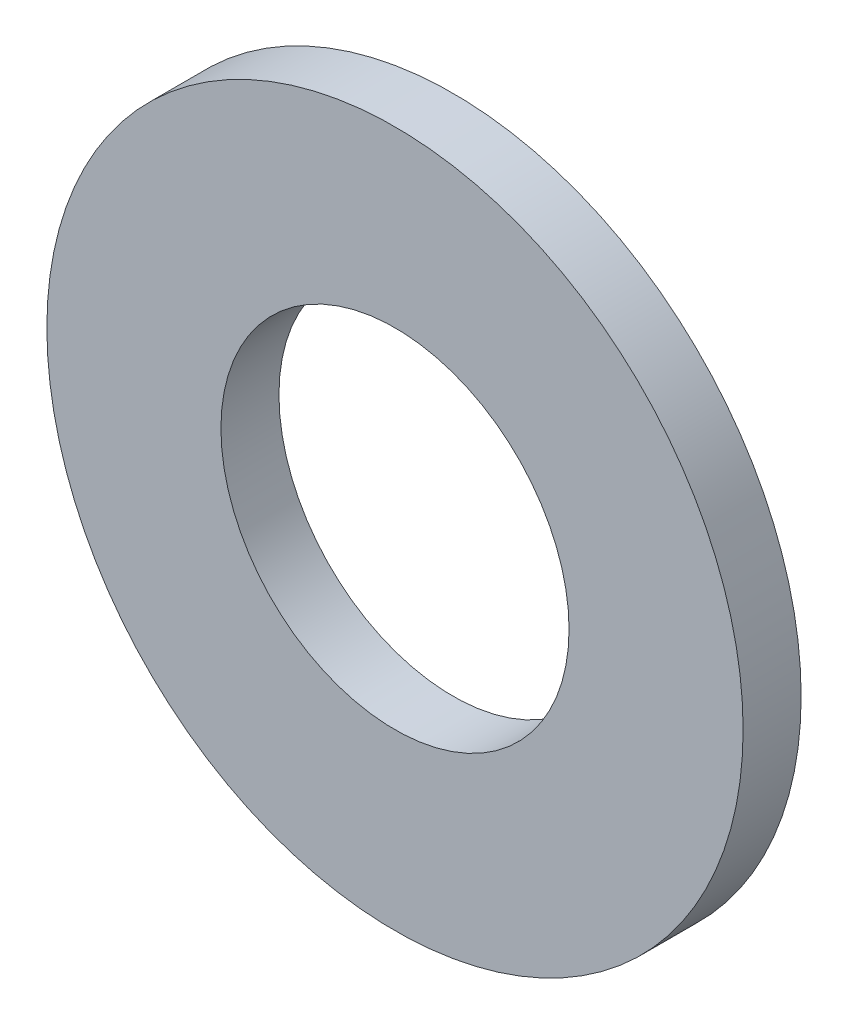
SolidWorks part; units mm, degrees
material "Aluminum Bronze"
ref_plane "Front Plane" through (0, 0, 0) normal (0, 0, 1) x (1, 0, 0)
ref_plane "Top Plane" through (0, 0, 0) normal (0, 1, 0) x (1, 0, 0)
ref_plane "Right Plane" through (0, 0, 0) normal (1, 0, 0) x (0, 0, -1)
sketch "Sketch1" plane through (0, 0, 0) normal (0, 0, 1) x (1, 0, 0)
  circle A0 centre (0, 0) radius 4.7625
  circle A1 centre (0, 0) radius 9.525
  dimension "D1" = 9.525
  dimension "D2" = 19.05
extrude "Boss-Extrude1" add sketch "Sketch1" along normal blind 1.5875
